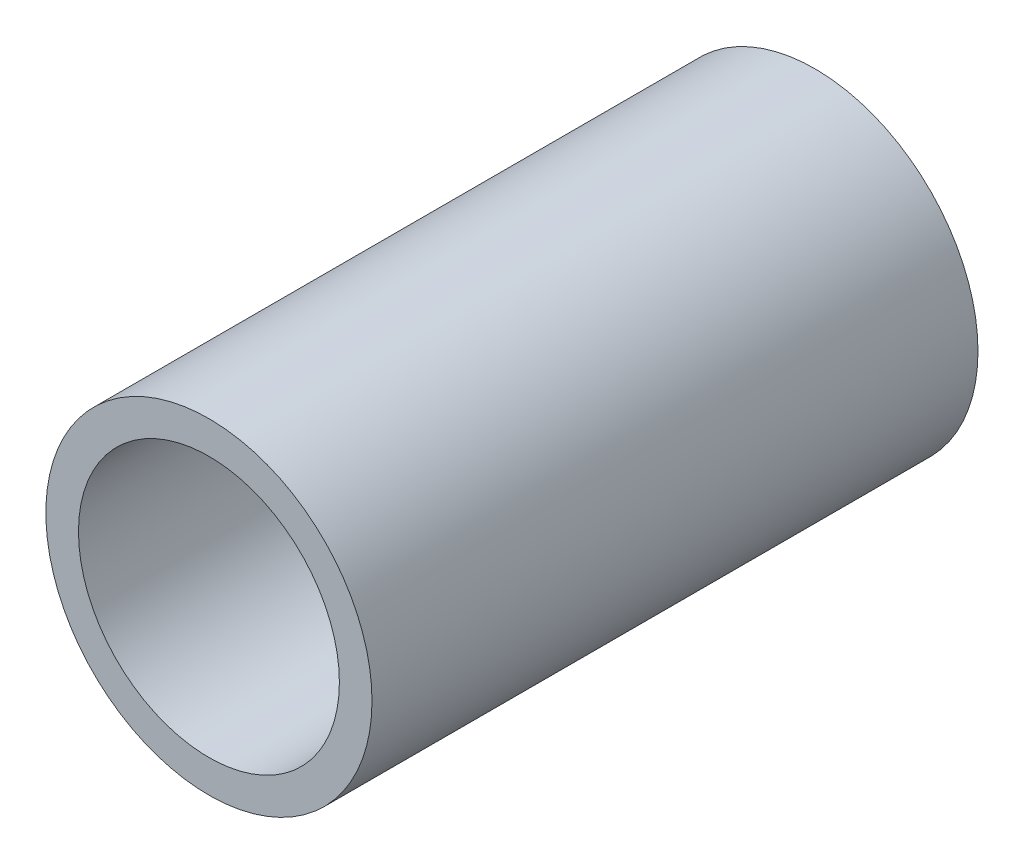
SolidWorks part; units mm, degrees
ref_plane "Front Plane" through (0, 0, 0) normal (0, 0, 1) x (1, 0, 0)
ref_plane "Top Plane" through (0, 0, 0) normal (0, 1, 0) x (1, 0, 0)
ref_plane "Right Plane" through (0, 0, 0) normal (1, 0, 0) x (0, 0, -1)
sketch "Sketch1" plane through (0, 0, 0) normal (0, 0, 1) x (1, 0, 0)
  circle A0 centre (0, 0) radius 1.25
  circle A1 centre (0, 0) radius 1
extrude "Boss-Extrude1" add sketch "Sketch1" along normal blind 4.645
equation "\"D1@Boss-Extrude1\"= \"HL@parametersSketch@prostheticParameters.SLDPRT\" * 0.117 - 4 - 3 - 10'Pinky MIP Tube"
